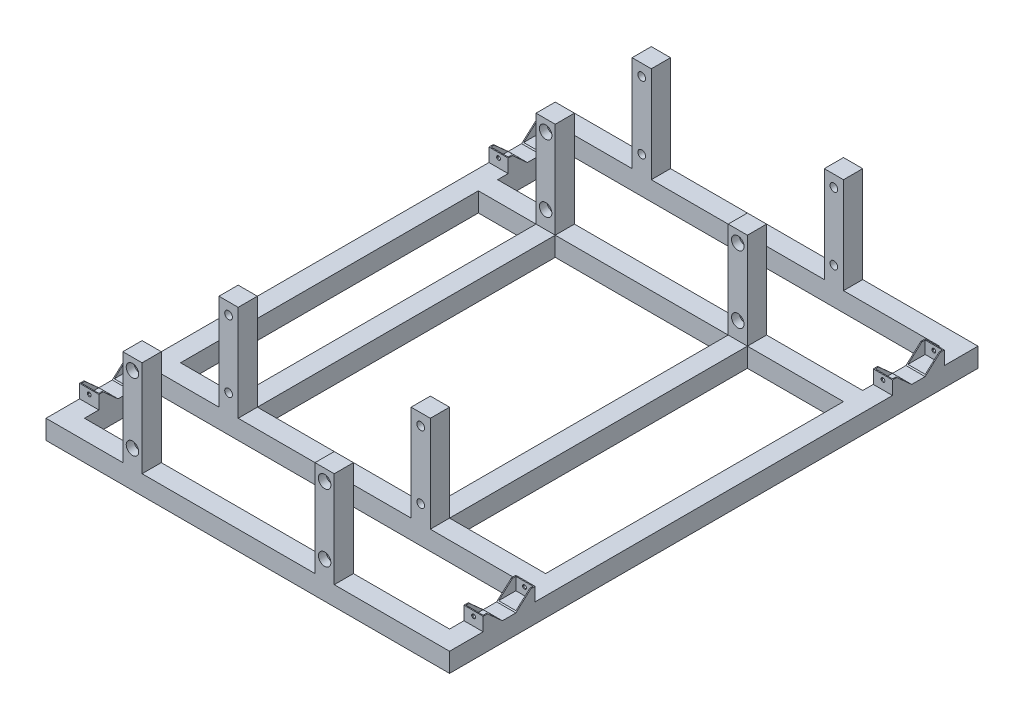
SolidWorks part; units mm, degrees
ref_plane "Front Plane" through (0, 0, 0) normal (0, 0, 1) x (1, 0, 0)
ref_plane "Top Plane" through (0, 0, 0) normal (0, 1, 0) x (1, 0, 0)
ref_plane "Right Plane" through (0, 0, 0) normal (1, 0, 0) x (0, 0, -1)
sketch "Sketch1" plane through (0, 0, 0) normal (0, 1, 0) x (1, 0, 0)
  line L0 (0, 165) -> (0, -106.787) construction
  line L1 (-190, 155) -> (-130, 155)
  line L2 (-190, 155) -> (-190, 175)
  line L3 (-190, 175) -> (190, 175)
  line L4 (190, 155) -> (190, 175)
  line L5 (-190, 155) -> (190, 175) construction
  line L6 (-190, 175) -> (190, 155) construction
  line L11 (-77.0852, 0) -> (77.0852, 0) construction
  line L12 (-190, -175) -> (190, -175)
  line L13 (190, -155) -> (190, -175)
  line L14 (-190, -155) -> (-130, -155)
  line L15 (-190, -155) -> (-190, -175)
  line L16 (90, -155) -> (190, -155)
  line L18 (-130, 155) -> (-130, -155)
  line L20 (-110, 155) -> (-110, -155)
  line L21 (-130, 155) -> (-110, -155) construction
  line L22 (-130, -155) -> (-110, 155) construction
  line L24 (70, 155) -> (70, -155)
  line L26 (90, 155) -> (90, -155)
  line L27 (70, 155) -> (90, -155) construction
  line L28 (70, -155) -> (90, 155) construction
  line L29 (-110, -155) -> (70, -155)
  line L30 (-110, 155) -> (70, 155)
  line L31 (90, 155) -> (190, 155)
  point P0 (0, 165)
  point P5 (0, -106.787)
  point P6 (80, 0)
  point P16 (-120, 0)
  dimension "D1" = 20
  dimension "D2" = 380
  dimension "D3" = 20
  dimension "D4" = 310
  dimension "D5" = 70
  dimension "D6" = 20
  dimension "D7" = 200
  dimension "D8" = 60
extrude "Boss-Extrude1" add sketch "Sketch1" along normal blind 20
sketch "Sketch2" plane through (0, 20, 0) normal (0, 1, 0) x (1, 0, 0)
  line L0 (190, 175) -> (-190, 175) construction
  line L1 (-130, 175) -> (-110, 175)
  line L2 (-130, 175) -> (-130, 155)
  line L3 (-130, 155) -> (-110, 155)
  line L4 (-110, 175) -> (-110, 155)
  line L5 (-130, 175) -> (-110, 155) construction
  line L6 (-130, 155) -> (-110, 175) construction
  line L7 (70, 155) -> (90, 155)
  line L8 (70, 155) -> (70, 175)
  line L9 (70, 175) -> (90, 175)
  line L10 (90, 155) -> (90, 175)
  line L11 (70, 155) -> (90, 175) construction
  line L12 (70, 175) -> (90, 155) construction
  line L13 (-190, 155) -> (-130, 155) construction
  line L15 (-110, 155) -> (-110, -155) construction
  line L16 (-130, 155) -> (-130, -155) construction
  line L17 (70, 155) -> (-110, 155) construction
  line L18 (70, -155) -> (70, 155) construction
  line L19 (90, -155) -> (90, 155) construction
  line L20 (-190, -175) -> (190, -175) construction
  line L21 (-130, -175) -> (-110, -175)
  line L22 (-130, -175) -> (-130, -155)
  line L23 (-130, -155) -> (-110, -155)
  line L24 (-110, -175) -> (-110, -155)
  line L25 (-130, -175) -> (-110, -155) construction
  line L26 (-130, -155) -> (-110, -175) construction
  line L27 (70, -155) -> (90, -155)
  line L28 (70, -155) -> (70, -175)
  line L29 (70, -175) -> (90, -175)
  line L30 (90, -155) -> (90, -175)
  line L31 (70, -155) -> (90, -175) construction
  line L32 (70, -175) -> (90, -155) construction
  line L33 (-110, -155) -> (70, -155) construction
  point P0 (-120, 165)
  point P5 (80, 165)
  point P24 (-120, -165)
  point P29 (80, -165)
extrude "Boss-Extrude2" add sketch "Sketch2" along normal blind 100
sketch "Sketch3" plane through (0, 20, 0) normal (0, 1, 0) x (1, 0, 0)
  line L0 (-190, 175) -> (-190, 155) construction
  line L1 (-210, 275) -> (-190, 275)
  line L2 (-210, 275) -> (-210, -275)
  line L3 (-210, -275) -> (-190, -275)
  line L4 (-190, 275) -> (-190, -275)
  line L5 (-210, 275) -> (-190, -275) construction
  line L6 (-210, -275) -> (-190, 275) construction
  line L7 (210, 275) -> (190, 275)
  line L8 (210, 275) -> (210, -275)
  line L9 (210, -275) -> (190, -275)
  line L10 (190, 275) -> (190, -275)
  line L11 (210, 275) -> (190, -275) construction
  line L12 (210, -275) -> (190, 275) construction
  line L13 (190, 155) -> (190, 175) construction
  line L14 (-130, 175) -> (-190, 175) construction
  line L15 (-190, -175) -> (-130, -175) construction
  line L16 (190, 175) -> (90, 175) construction
  line L17 (90, -175) -> (190, -175) construction
  point P0 (-200, 0)
  point P5 (200, 0)
  dimension "D1" = 20
  dimension "D2" = 20
  dimension "D3" = 550
  dimension "D4" = 550
  dimension "D5" = 100
  dimension "D6" = 100
  dimension "D7" = 100
  dimension "D8" = 100
extrude "Boss-Extrude3" add sketch "Sketch3" against normal up to surface (20 mm away) up to face at (-6.6667, 0, 0)
sketch "Sketch4" plane through (0, 20, 0) normal (0, 1, 0) x (1, 0, 0)
  line L0 (-85.7578, 0) -> (53.8118, 0) construction
  line L1 (-190, 275) -> (190, 275)
  line L2 (-190, 275) -> (-190, 255)
  line L3 (-190, 255) -> (190, 255)
  line L4 (190, 275) -> (190, 255)
  line L5 (-190, 275) -> (190, 255) construction
  line L6 (-190, 255) -> (190, 275) construction
  line L7 (-190, 275) -> (-210, 275) construction
  line L8 (-190, 175) -> (-190, 275) construction
  line L9 (190, 275) -> (190, 175) construction
  line L10 (-190, -255) -> (190, -255)
  line L11 (190, -275) -> (190, -255)
  line L12 (-190, -275) -> (190, -275)
  line L13 (-190, -275) -> (-190, -255)
  line L14 (-190, -275) -> (-190, -175) construction
  line L15 (-210, -275) -> (-190, -275) construction
  line L16 (190, -275) -> (210, -275) construction
  line L17 (190, -175) -> (190, -275) construction
  point P0 (0, 265)
  dimension "D1" = 20
  dimension "D2" = 380
extrude "Boss-Extrude4" add sketch "Sketch4" against normal up to surface (20 mm away) up to face at (0, 0, 0)
sketch "Sketch5" plane through (0, 20, 0) normal (0, 1, 0) x (1, 0, 0)
  line L0 (190, -255) -> (-190, -255) construction
  line L1 (-130, 275) -> (-110, 275)
  line L2 (-130, 275) -> (-130, 255)
  line L3 (-130, 255) -> (-110, 255)
  line L4 (-110, 275) -> (-110, 255)
  line L5 (-130, 275) -> (-110, 255) construction
  line L6 (-130, 255) -> (-110, 275) construction
  line L7 (70, 275) -> (90, 275)
  line L8 (70, 275) -> (70, 255)
  line L9 (70, 255) -> (90, 255)
  line L10 (90, 275) -> (90, 255)
  line L11 (70, 275) -> (90, 255) construction
  line L12 (70, 255) -> (90, 275) construction
  line L13 (-130, -255) -> (-110, -255)
  line L14 (-130, -255) -> (-130, -275)
  line L15 (-130, -275) -> (-110, -275)
  line L16 (-110, -255) -> (-110, -275)
  line L17 (-130, -255) -> (-110, -275) construction
  line L18 (-130, -275) -> (-110, -255) construction
  line L19 (70, -255) -> (90, -255)
  line L20 (70, -255) -> (70, -275)
  line L21 (70, -275) -> (90, -275)
  line L22 (90, -255) -> (90, -275)
  line L23 (70, -255) -> (90, -275) construction
  line L24 (70, -275) -> (90, -255) construction
  line L25 (-210, -275) -> (210, -275) construction
  line L26 (-110, -175) -> (-110, -155) construction
  line L27 (-130, -155) -> (-130, -175) construction
  line L28 (90, -175) -> (90, -155) construction
  line L29 (70, -155) -> (70, -175) construction
  line L30 (210, 275) -> (-210, 275) construction
  line L31 (-190, 255) -> (190, 255) construction
  line L32 (90, 155) -> (90, 175) construction
  line L33 (70, 175) -> (70, 155) construction
  line L34 (-110, 155) -> (-110, 175) construction
  line L35 (-130, 175) -> (-130, 155) construction
  point P0 (-120, 265)
  point P5 (80, 265)
  point P10 (-120, -265)
  point P15 (80, -265)
extrude "Boss-Extrude5" add sketch "Sketch5" along normal blind 100
sketch "Sketch7" plane through (0, 0, -275) normal (0, 0, -1) x (-1, 0, 0)
  line L0 (120, 120) -> (120, 0) construction
  line L1 (110, 120) -> (130, 120) construction
  line L2 (-210, 0) -> (210, 0) construction
  line L3 (102.2662, 60) -> (134.3764, 60) construction
  line L4 (-70, 20) -> (110, 20) construction
  line L5 (120, 108) -> (-90, 108) construction
  line L6 (-90, 120) -> (-90, 20) construction
  line L7 (120, 38) -> (-90, 38) construction
  line L8 (-80, 120) -> (-80, 0) construction
  line L9 (-90, 120) -> (-70, 120) construction
  line L10 (-210, 20) -> (-90, 20) construction
  circle A0 centre (120, 108) radius 4
  circle A1 centre (120, 108) radius 6.5 construction
  circle A2 centre (120, 38) radius 6.4 construction
  circle A3 centre (120, 38) radius 4
  circle A4 centre (-80, 108) radius 4
  circle A5 centre (-80, 38) radius 4
  circle A6 centre (-80, 38) radius 6.5 construction
  circle A7 centre (-80, 108) radius 6.5 construction
  dimension "D1" = 12
  dimension "D2" = 18
  dimension "D3" = 12
  dimension "D4" = 18
extrude "Cut-Extrude1" cut sketch "Sketch7" against normal up to surface (550 mm away) up to face at (-13.3333, 50, 275)
sketch "Sketch8" plane through (0, 0, -275) normal (0, 0, -1) x (-1, 0, 0)
  line L0 (120, 42) -> (120, 34) construction
  line L1 (120, 112) -> (120, 104) construction
  line L3 (-80, 42) -> (-80, 34) construction
  circle A1 centre (-80, 38) radius 6.5
  circle A2 centre (120, 108) radius 6.5
  circle A3 centre (120, 38) radius 6.5
  circle A4 centre (120, 38) radius 4 construction
  circle A5 centre (120, 108) radius 4 construction
  circle A7 centre (-80, 38) radius 4 construction
  circle A8 centre (-80, 108) radius 6.5
  point P19 (120, 108)
  point P21 (120, 38)
  point P28 (-80, 38)
extrude "Cut-Extrude2" cut sketch "Sketch8" against normal blind 8
ref_plane "Plane1" through (0, 0, -215) normal (0, 0, -1) x (-1, 0, 0)
mirror "Mirror1" about plane through (0, 0, -215) normal (0, 0, -1) of "Cut-Extrude2"
sketch "Sketch9" plane through (0, 0, 275) normal (0, 0, 1) x (1, 0, 0)
  circle A0 centre (-120, 108) radius 6.5
  circle A1 centre (-120, 38) radius 6.5
  circle A2 centre (80, 108) radius 6.5
  circle A3 centre (80, 38) radius 6.5
extrude "Cut-Extrude3" cut sketch "Sketch9" against normal blind 8
ref_plane "Plane2" through (0, 0, 215) normal (0, 0, 1) x (1, 0, 0)
mirror "Mirror2" about plane through (0, 0, 215) normal (0, 0, 1) of "Cut-Extrude3"
sketch "Sketch10" plane through (-210, 0, 0) normal (-1, 0, 0) x (0, 0, 1)
  line L0 (-240, 20) -> (-240, 38)
  line L1 (-275, 20) -> (275, 20) construction
  line L2 (-240, 38) -> (-220, 20)
  line L3 (-220, 20) -> (-240, 20)
  line L4 (-206, 20) -> (-186, 20)
  line L5 (-186, 20) -> (-186, 38)
  line L6 (-186, 38) -> (-206, 20)
  line L7 (-275, 0) -> (-275, 20) construction
  dimension "D1" = 20
  dimension "D2" = 18
  dimension "D3" = 18
  dimension "20" = 20
  dimension "D4" = 35
  dimension "D5" = 14
extrude "Boss-Extrude6" add sketch "Sketch10" against normal up to surface (400 mm away)
ref_plane "Plane3" through (0, 42, 0) normal (0, -1, 0) x (-1, 0, 0)
sketch "Sketch11" plane through (0, 42, 0) normal (0, -1, 0) x (-1, 0, 0)
  line L0 (200, 240) -> (200, 220) construction
  line L1 (190, 240) -> (210, 240) construction
  line L2 (190, 220) -> (210, 220) construction
  line L3 (210, 230) -> (190, 230) construction
  line L4 (210, 220) -> (210, 240) construction
  line L5 (190, 220) -> (190, 240) construction
  line L6 (200, 206) -> (200, 186) construction
  line L7 (190, 206) -> (210, 206) construction
  line L8 (190, 186) -> (210, 186) construction
  line L9 (210, 196) -> (190, 196) construction
  line L10 (210, 186) -> (210, 206) construction
  line L11 (190, 186) -> (190, 206) construction
  line L12 (190, 240) -> (210, 240) construction
  line L13 (209, 239) -> (191, 239)
  line L14 (209, 239) -> (209, 221)
  line L15 (209, 221) -> (191, 221)
  line L16 (191, 239) -> (191, 221)
  line L17 (209, 239) -> (191, 221) construction
  line L18 (209, 221) -> (191, 239) construction
  line L19 (209, 205) -> (191, 205)
  line L20 (209, 205) -> (209, 187)
  line L21 (209, 187) -> (191, 187)
  line L22 (191, 205) -> (191, 187)
  line L23 (209, 205) -> (191, 187) construction
  line L24 (209, 187) -> (191, 205) construction
  point P24 (200, 230)
  point P29 (200, 196)
  dimension "D1" = 1
  dimension "D2" = 1
  dimension "1" = 1
  dimension "D3" = 1
extrude "Cut-Extrude4" cut sketch "Sketch11" along normal blind 21
ref_plane "Plane4" through (0, 0, 0) normal (0, 0, -1) x (-1, 0, 0)
mirror "Mirror3" about plane through (0, 0, 0) normal (0, 0, -1) of "Boss-Extrude6", "Cut-Extrude4"
ref_plane "Plane5" through (0, 0, 0) normal (-1, 0, 0) x (0, 0, 1)
mirror "Mirror5" about plane through (0, 0, 0) normal (-1, 0, 0) of "Mirror3", "Boss-Extrude6", "Cut-Extrude4"
ref_plane "Plane6" through (-190, 0, 0) normal (-1, 0, 0) x (0, 0, 1)
sketch "Sketch12" plane through (-190, 0, 0) normal (-1, 0, 0) x (0, 0, 1)
  line L0 (-220, 20) -> (-240, 20)
  line L1 (-240, 20) -> (-240, 38)
  line L2 (-240, 38) -> (-220, 20)
  line L3 (-186, 38) -> (-186, 20)
  line L4 (-186, 20) -> (-206, 20)
  line L5 (-206, 20) -> (-186, 38)
  line L7 (186, 20) -> (206, 20)
  line L9 (240, 38) -> (240, 20)
  line L10 (240, 20) -> (220, 20)
  line L11 (220, 20) -> (240, 38)
  line L13 (186, 38) -> (206, 20)
  line L14 (186, 38) -> (186, 20)
extrude "Cut-Extrude5" cut sketch "Sketch12" against normal up to surface (380 mm away) up to face at (190, 10, 0)
sketch "Sketch13" plane through (0, 0, 240) normal (0, 0, 1) x (1, 0, 0)
  line L0 (200, 20) -> (200, 38) construction
  line L1 (190, 20) -> (210, 20) construction
  line L2 (210, 38) -> (190, 38) construction
  circle A0 centre (200, 29) radius 2
  dimension "D1" = 4
extrude "Cut-Extrude6" cut sketch "Sketch13" against normal up to surface (480 mm away) up to face at (-200, 29, -240)
sketch "Sketch14" plane through (0, 0, 240) normal (0, 0, 1) x (1, 0, 0)
  line L0 (-200, 38) -> (-200, 20) construction
  line L1 (-190, 38) -> (-210, 38) construction
  line L2 (-190, 20) -> (-210, 20) construction
  line L4 (-210, 38) -> (-210, 20) construction
  circle A0 centre (-200, 29) radius 2
extrude "Cut-Extrude7" cut sketch "Sketch14" against normal up to surface (480 mm away) up to face at (-200, 29, -240)
sketch "Sketch15" plane through (-130, 0, 0) normal (-1, 0, 0) x (0, 0, 1)
  line L0 (175, 120) -> (175, 20) construction
  line L1 (175, 87.6293) -> (255, 87.6293) construction
  line L2 (255, 120) -> (255, 20) construction
  line L3 (186, 38) -> (186, 118) construction
  dimension "D1" = 80
  dimension "D2" = 80
sketch "Sketch18" plane through (0, 0, 275) normal (0, 0, 1) x (1, 0, 0)
  line L0 (-190, 38) -> (-190, 34)
  line L2 (-190, 20) -> (-190, 38) construction
  line L3 (-190, 34) -> (-210, 34)
  line L4 (-210, 38) -> (-210, 20) construction
  line L5 (-210, 34) -> (-210, 38)
  line L6 (-210, 38) -> (-190, 38)
  line L7 (0, 0) -> (0, 99.8106) construction
  line L8 (210, 38) -> (190, 38)
  line L9 (210, 34) -> (210, 38)
  line L10 (190, 34) -> (210, 34)
  line L11 (190, 38) -> (190, 34)
  dimension "D1" = 4
extrude "Cut-Extrude8" cut sketch "Sketch18" against normal up to surface (515 mm away) up to face at (-202, 29, -240)
